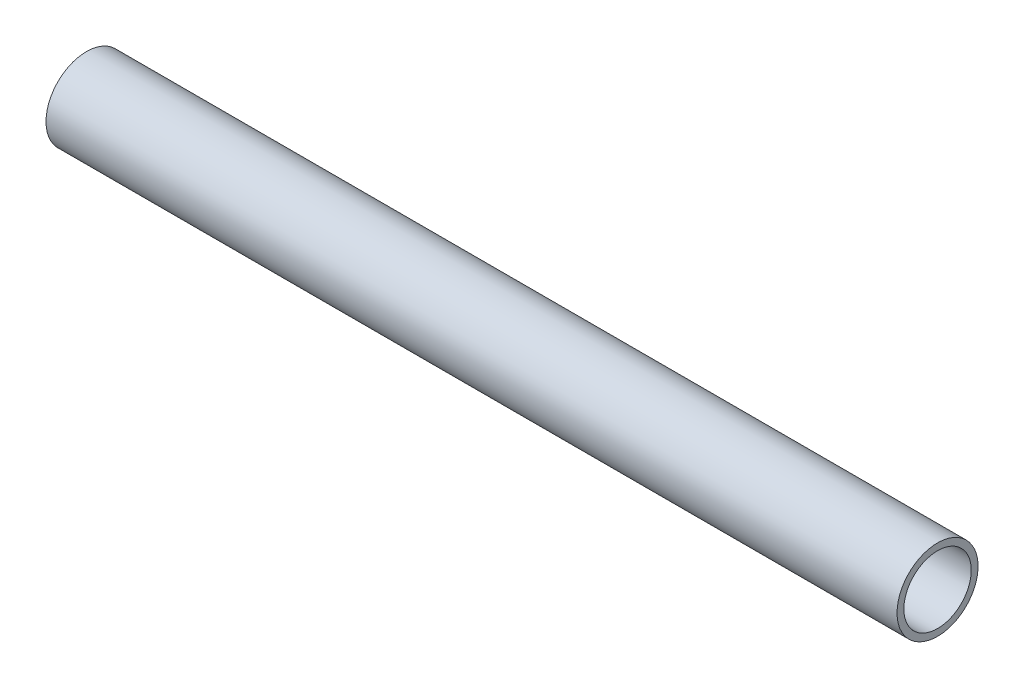
SolidWorks part; units mm, degrees
ref_plane "Front Plane" through (0, 0, 0) normal (0, 0, 1) x (1, 0, 0)
ref_plane "Top Plane" through (0, 0, 0) normal (0, 1, 0) x (1, 0, 0)
ref_plane "Right Plane" through (0, 0, 0) normal (1, 0, 0) x (0, 0, -1)
sketch "Sketch1" plane through (0, 0, 0) normal (0, 0, 1) x (1, 0, 0)
  line L0 (158.5678, 670.5289) -> (25.2028, 670.5289)
  point P2 (158.5678, 670.5289)
other "Pipe 0.5 SCH 40(1)"
ref_plane "Plane1" through (158.5678, 670.5289, 0) normal (-1, 0, 0) x (0, -1, 0)
sketch "Sketch11" plane through (158.5678, 670.5289, 0) normal (-1, 0, 0) x (0, -1, 0)
  circle A0 centre (0, 0) radius 5.2832
  circle A1 centre (0, 0) radius 6.35
  point P5 (0, 0)
  dimension "D1" = 12.7
  dimension "D2" = 10.5664
